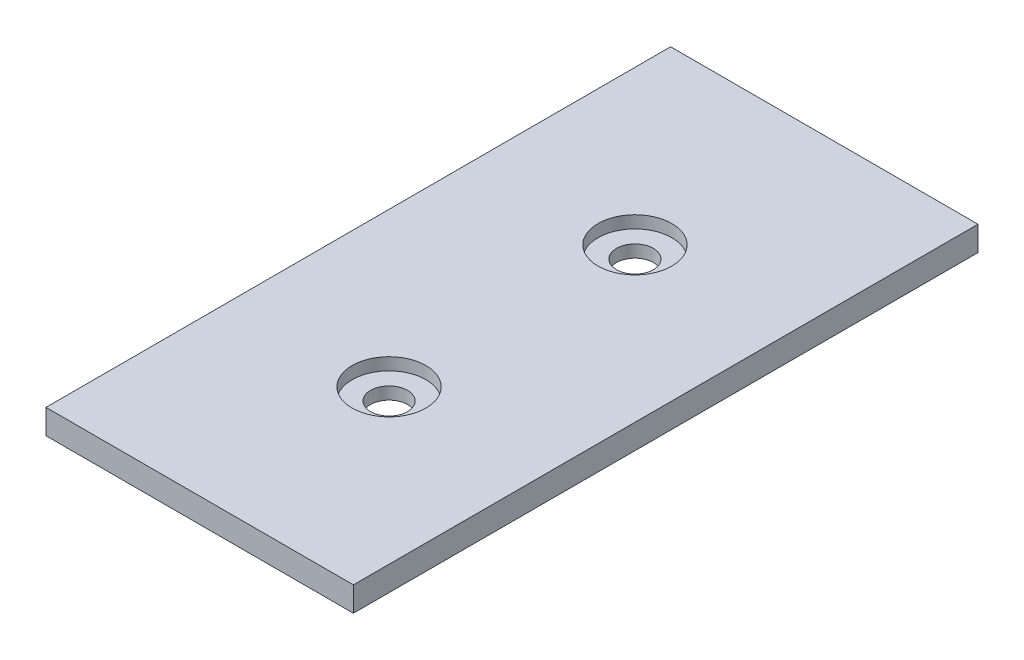
SolidWorks part; units mm, degrees
material "Custom Plastic"
ref_plane "Front Plane" through (0, 0, 0) normal (0, 0, 1) x (1, 0, 0)
ref_plane "Top Plane" through (0, 0, 0) normal (0, 1, 0) x (1, 0, 0)
ref_plane "Right Plane" through (0, 0, 0) normal (1, 0, 0) x (0, 0, -1)
sketch "Sketch1" plane through (0, 0, 0) normal (0, 1, 0) x (1, 0, 0)
  line L1 (-25, -50.8) -> (25, -50.8)
  line L2 (-25, -50.8) -> (-25, 50.8)
  line L3 (-25, 50.8) -> (25, 50.8)
  line L4 (25, -50.8) -> (25, 50.8)
  line L5 (-25, -50.8) -> (25, 50.8) construction
  line L6 (-25, 50.8) -> (25, -50.8) construction
  point P0 (0, 0)
  dimension "D1" = 101.6
  dimension "D2" = 50
extrude "Boss-Extrude1" add sketch "Sketch1" along normal blind 4
sketch "Sketch2" plane through (0, 4, 0) normal (0, 1, 0) x (1, 0, 0)
  line L0 (-200.1557, 0) -> (201.6998, 0) construction
  circle A0 centre (0, 20) radius 3
  circle A1 centre (0, -20) radius 3
  dimension "D1" = 6
  dimension "D2" = 20
extrude "Cut-Extrude1" cut sketch "Sketch2" against normal blind 10
sketch "Sketch3" plane through (0, 4, 0) normal (0, 1, 0) x (1, 0, 0)
  circle A0 centre (0, 20) radius 6
  circle A1 centre (0, -20) radius 6
  dimension "D1" = 12
extrude "Cut-Extrude2" cut sketch "Sketch3" against normal blind 2 contours A0 | A1
